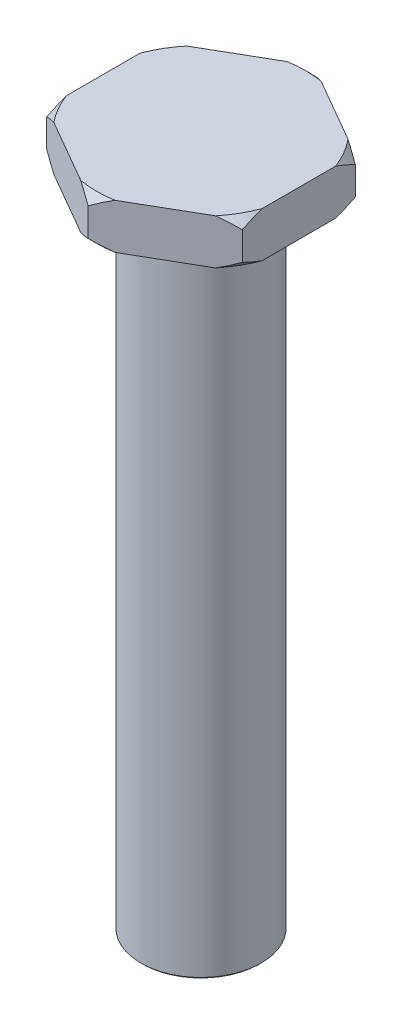
SolidWorks part; units mm, degrees
ref_plane "前视基准面" through (0, 0, 0) normal (0, 0, 1) x (1, 0, 0)
ref_plane "上视基准面" through (0, 0, 0) normal (0, 1, 0) x (1, 0, 0)
ref_plane "右视基准面" through (0, 0, 0) normal (1, 0, 0) x (0, 0, -1)
sketch "草图1" plane through (0, 0, 0) normal (0, 1, 0) x (1, 0, 0)
  line L1 (0, 7.5056) -> (-6.5, 3.7528)
  line L2 (-6.5, 3.7528) -> (-6.5, -3.7528)
  line L3 (-6.5, -3.7528) -> (0, -7.5056)
  line L4 (0, -7.5056) -> (6.5, -3.7528)
  line L5 (6.5, -3.7528) -> (6.5, 3.7528)
  line L6 (6.5, 3.7528) -> (0, 7.5056)
  circle A0 centre (0, 0) radius 6.5 construction
  dimension "D1" = 13
extrude "凸台-拉伸1" add sketch "草图1" along normal blind 3
sketch "草图2" plane through (0, 0, 0) normal (0, -1, 0) x (1, 0, 0)
  circle A0 centre (0, 0) radius 4
extrude "凸台-拉伸2" add sketch "草图2" along normal blind 43
cosmetic thread "装饰螺纹线1" parameters "D1"=15, "D2"=6.891
chamfer "倒角1" distance 0.1 angle 45 1 edges at (0, -43, -4)
sketch "草图4" plane through (0, 0, 0) normal (0, 0, 1) x (1, 0, 0)
  line L0 (0, 3) -> (0, -12.3788) construction
sketch "草图5" plane through (0, 0, 0) normal (1, 0, 0) x (0, 0, -1)
  line L0 (-6.9456, 3) -> (-7.5056, 2.44)
  line L1 (-7.5056, 3) -> (-3.7528, 3) construction
  line L2 (-7.5056, 3) -> (-7.5056, 0) construction
  line L3 (-7.5056, 2.44) -> (-7.5056, 3)
  line L4 (-7.5056, 3) -> (-6.9456, 3)
  line L5 (-7.5056, 0) -> (-7.5056, 0.56)
  line L6 (-7.5056, 0.56) -> (-6.9456, 0)
  line L7 (-7.5056, 0) -> (-3.7528, 0) construction
  line L8 (-6.9456, 0) -> (-7.5056, 0)
  line L9 (0, 3) -> (0, 7.2877) construction
  line L10 (-3.7528, 3) -> (3.7528, 3) construction
revolve "切除-旋转2" cut sketch "草图5" angle 360 about L9
